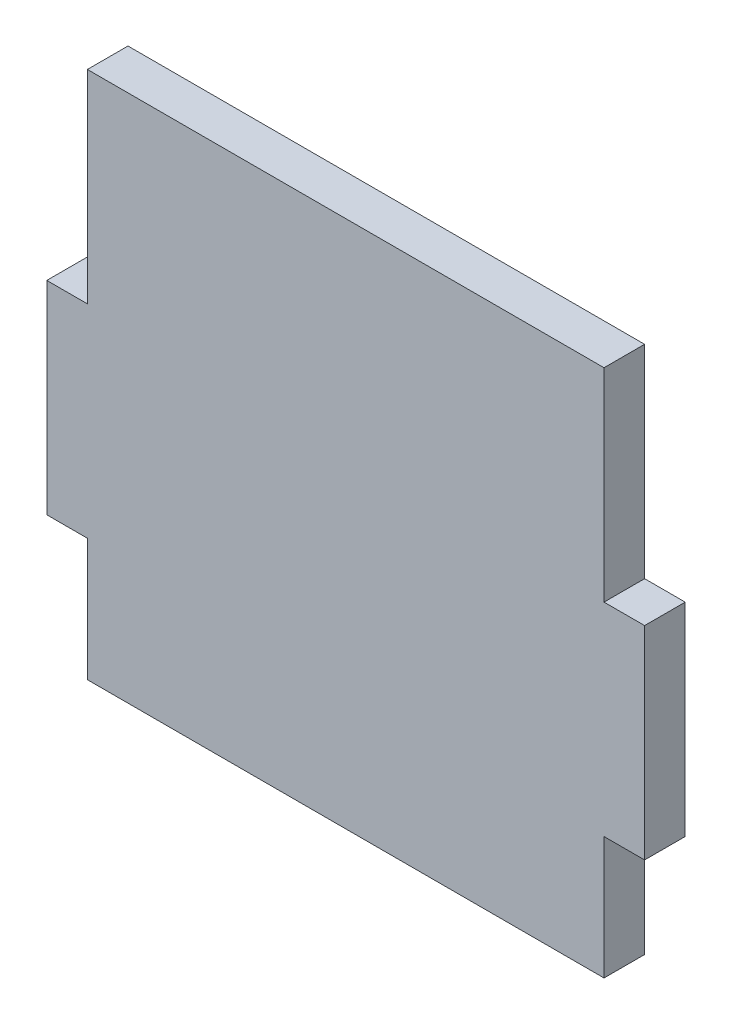
SolidWorks part; units mm, degrees
ref_plane "Спереди" through (0, 0, 0) normal (0, 0, 1) x (1, 0, 0)
ref_plane "Сверху" through (0, 0, 0) normal (0, 1, 0) x (1, 0, 0)
ref_plane "Справа" through (0, 0, 0) normal (1, 0, 0) x (0, 0, -1)
sketch "Эскиз1" plane through (0, 0, 0) normal (0, 0, 1) x (1, 0, 0)
  line L1 (0, 0) -> (-50.9, 0)
  line L2 (0, 0) -> (0, -89.0716)
  line L3 (-50.9, -89.0716) -> (0, -89.0716)
  line L4 (-50.9, 0) -> (-50.9, -89.0716)
  line L8 (-50.9, -40) -> (-54.9, -40)
  line L9 (-50.9, 0) -> (-54.9, 0)
  line L10 (-50.9, 0) -> (-50.9, -20)
  line L11 (-50.9, -20) -> (-54.9, -20)
  line L12 (-54.9, 0) -> (-54.9, -20)
  line L13 (-50.9, -40) -> (-50.9, -60)
  line L14 (-50.9, -60) -> (-54.9, -60)
  line L15 (-54.9, -40) -> (-54.9, -60)
  line L24 (-25.45, 0) -> (-25.45, -89.0716) construction
  line L29 (4, -40) -> (4, -60)
  line L30 (0, -60) -> (4, -60)
  line L31 (0, -40) -> (0, -60)
  line L32 (4, 0) -> (4, -20)
  line L33 (0, -20) -> (4, -20)
  line L34 (0, 0) -> (0, -20)
  line L35 (0, 0) -> (4, 0)
  line L36 (0, -40) -> (4, -40)
  line L39 (-2.6452, -82.4264) -> (4, -89.0716) construction
  line L41 (-50.9, -80) -> (-54.9, -80) [skipped]
  line L42 (-50.9, -80) -> (-50.9, -100) [skipped]
  line L43 (-50.9, -100) -> (-54.9, -100) [skipped]
  line L44 (-54.9, -80) -> (-54.9, -100) [skipped]
  dimension "D1" = 50.9
  dimension "D2" = 20
  dimension "D8" = 20
  dimension "D9" = 4
  dimension "D10" = 3
extrude "Бобышка-Вытянуть1" add sketch "Эскиз1" along normal blind 4
sketch "Эскиз2" plane through (0, 0, 0) normal (0, 0, -1) x (-1, 0, 0)
  line L1 (54.9, -20) -> (-15.8616, -20)
  line L2 (54.9, -20) -> (54.9, 8.5171)
  line L3 (54.9, 8.5171) -> (-15.8616, 8.5171)
  line L4 (-15.8616, -20) -> (-15.8616, 8.5171)
extrude "Вырез-Вытянуть1" cut sketch "Эскиз2" against normal blind 4
sketch "Эскиз3" plane through (0, 0, 0) normal (0, 0, -1) x (-1, 0, 0)
  line L1 (50.9, -89.0716) -> (-19.0665, -89.0716)
  line L2 (50.9, -89.0716) -> (50.9, -72.0716)
  line L3 (50.9, -72.0716) -> (-19.0665, -72.0716)
  line L4 (-19.0665, -89.0716) -> (-19.0665, -72.0716)
  dimension "D1" = 17
extrude "Вырез-Вытянуть2" cut sketch "Эскиз3" against normal blind 10
